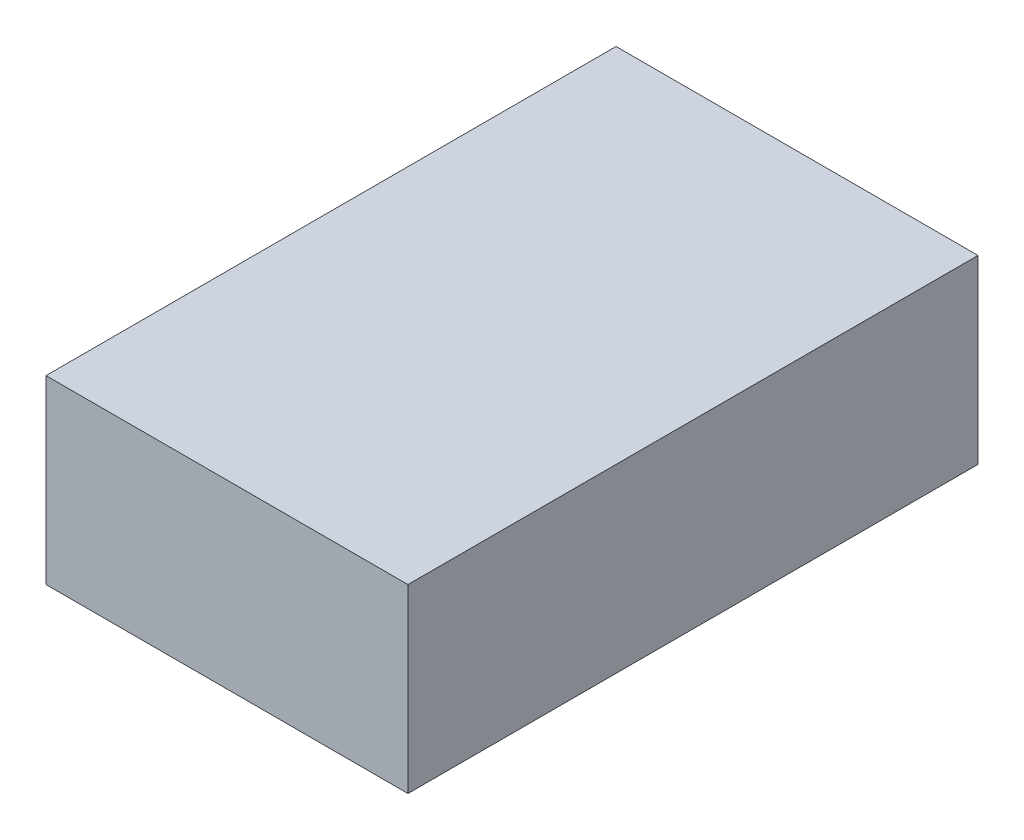
SolidWorks part; units mm, degrees
ref_plane "Front" through (0, 0, 0) normal (0, 0, 1) x (1, 0, 0)
ref_plane "Top" through (0, 0, 0) normal (0, 1, 0) x (1, 0, 0)
ref_plane "Right" through (0, 0, 0) normal (1, 0, 0) x (0, 0, -1)
sketch "草图1" plane through (0, 0, 0) normal (0, 1, 0) x (1, 0, 0)
  line L0 (0, 0) -> (40, 0) construction
  line L1 (40, 0) -> (40, -63) construction
  line L2 (40, -63) -> (0, -63) construction
  line L3 (0, -63) -> (0, 0) construction
  line L4 (0, 0) -> (40, 0)
  line L5 (40, 0) -> (40, -63)
  line L6 (40, -63) -> (0, -63)
  line L7 (0, -63) -> (0, 0)
extrude "凸台-拉伸1" add sketch "草图1" along normal blind 20
